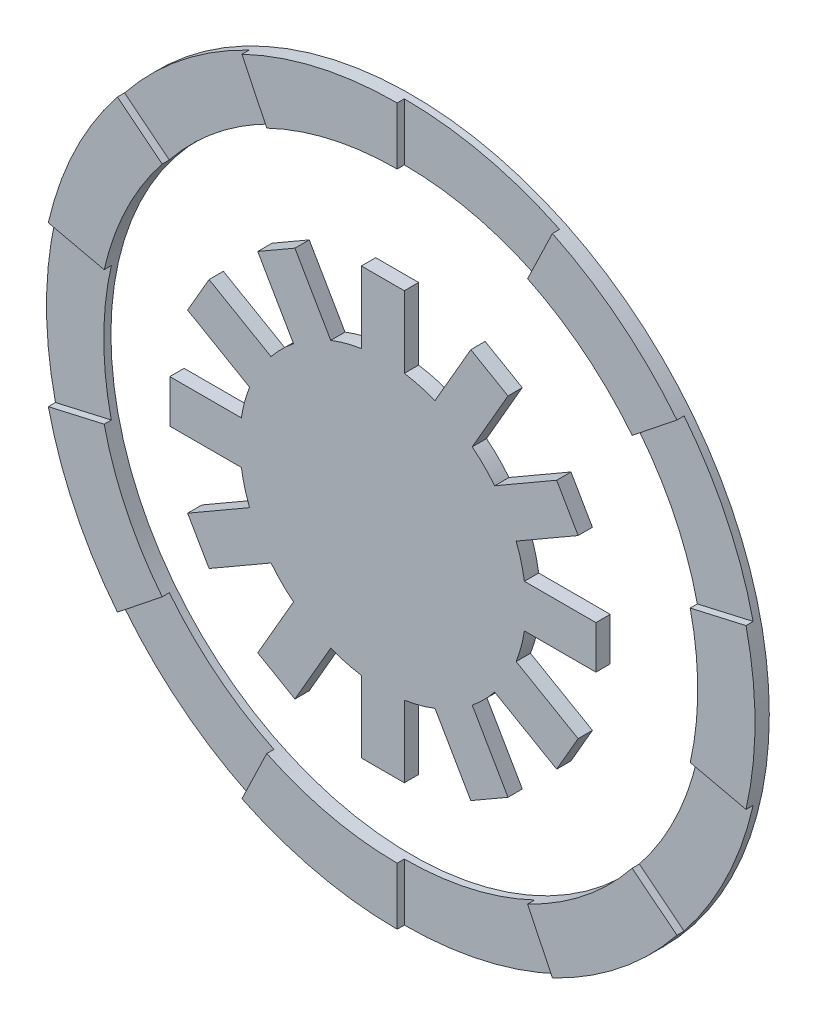
SolidWorks part; units mm, degrees
ref_plane "正面" through (0, 0, 0) normal (0, 0, 1) x (1, 0, 0)
ref_plane "平面" through (0, 0, 0) normal (0, 1, 0) x (1, 0, 0)
ref_plane "右側面" through (0, 0, 0) normal (1, 0, 0) x (0, 0, -1)
sketch "ｽｹｯﾁ1" plane through (0, 0, 0) normal (0, 0, 1) x (1, 0, 0)
  circle A0 centre (0, 0) radius 50
  circle A1 centre (0, 0) radius 42
  dimension "D1" = 100
  dimension "D2" = 8
extrude "ﾎﾞｽ - 押し出し1" add sketch "ｽｹｯﾁ1" along normal blind 2
sketch "ｽｹｯﾁ2" plane through (0, 0, 2) normal (0, 0, 1) x (1, 0, 0)
  line L0 (0, 50) -> (0, 42)
  line L1 (0, 0) -> (21.6942, 45.0484) construction
  line L2 (21.6942, 45.0484) -> (18.2231, 37.8407)
  circle A0 centre (0, 0) radius 50 construction
  circle A1 centre (0, 0) radius 42 construction
  arc A2 (21.6942, 45.0484) -> (0, 50) centre (0, 0) ccw
  arc A3 (18.2231, 37.8407) -> (0, 42) centre (0, 0) ccw
  dimension "D1" = 25.714
extrude "ｶｯﾄ - 押し出し1" cut sketch "ｽｹｯﾁ2" against normal blind 1
pattern_circular "円形ﾊﾟﾀｰﾝ1" count 7 over 360 about axis through (0, 0, 0) along (0, 0, 1) of "ｶｯﾄ - 押し出し1"
sketch "ｽｹｯﾁ3" plane through (0, 0, 2) normal (0, 0, 1) x (1, 0, 0)
  circle A0 centre (0, 0) radius 20
  dimension "D1" = 40
extrude "ﾎﾞｽ - 押し出し2" add sketch "ｽｹｯﾁ3" along normal blind 2 separate body
sketch "ｽｹｯﾁ4" plane through (0, 0, 4) normal (0, 0, 1) x (1, 0, 0)
  line L0 (0, 0) -> (0, 29.7737) construction
  line L1 (3, 29.7737) -> (-3, 29.7737)
  line L2 (-3, 29.7737) -> (-3, 19.7737)
  line L3 (3, 29.7737) -> (3, 19.7737)
  circle A0 centre (0, 0) radius 20 construction
  circle A2 centre (0, 0) radius 20
  arc A3 (3, 19.7737) -> (-3, 19.7737) centre (0, 0) ccw
  dimension "D1" = 3
  dimension "D2" = 10
  dimension "D3" = 0
extrude "ﾎﾞｽ - 押し出し3" add sketch "ｽｹｯﾁ4" against normal blind 2
pattern_circular "円形ﾊﾟﾀｰﾝ2" count 12 over 360 about axis through (0, 0, 0) along (0, 0, 1) of "ﾎﾞｽ - 押し出し3"
equation "\"D1@ｽｹｯﾁ2\"=360/14"
